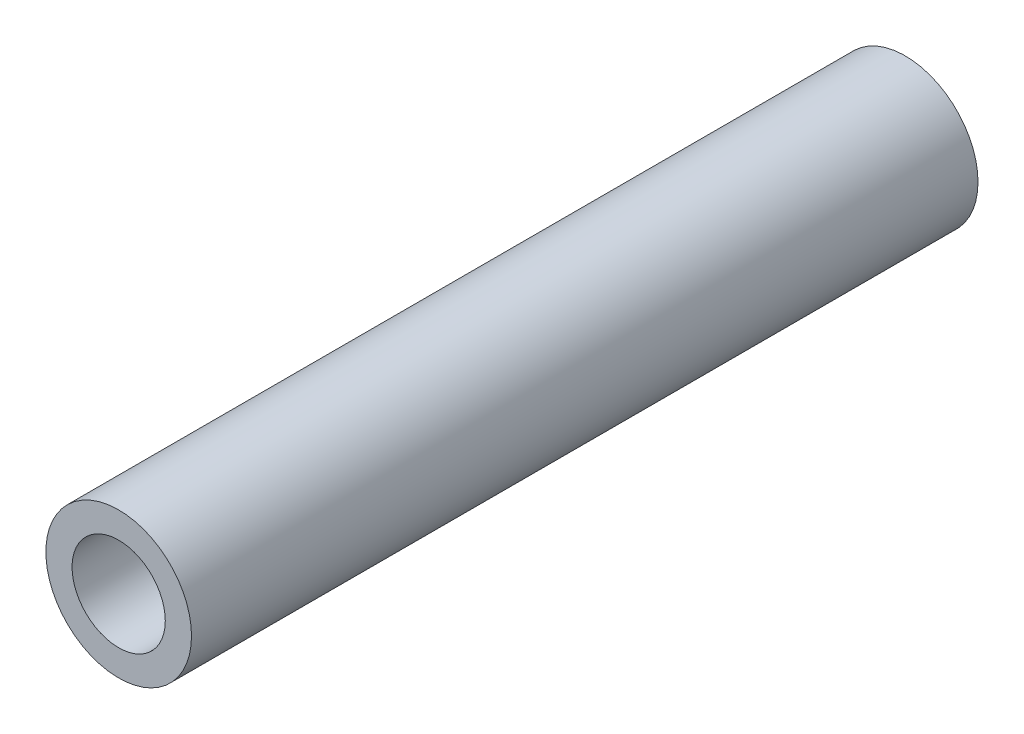
SolidWorks part; units mm, degrees
ref_plane "Front" through (0, 0, 0) normal (0, 0, 1) x (1, 0, 0)
ref_plane "Top" through (0, 0, 0) normal (0, 1, 0) x (1, 0, 0)
ref_plane "Right" through (0, 0, 0) normal (1, 0, 0) x (0, 0, -1)
sketch "Sketch1" plane through (0, 0, 0) normal (0, 0, 1) x (1, 0, 0)
  circle A0 centre (0, 0) radius 1.6
  circle A1 centre (0, 0) radius 2.5
extrude "Boss-Extrude3" add sketch "Sketch1" along normal blind 27
